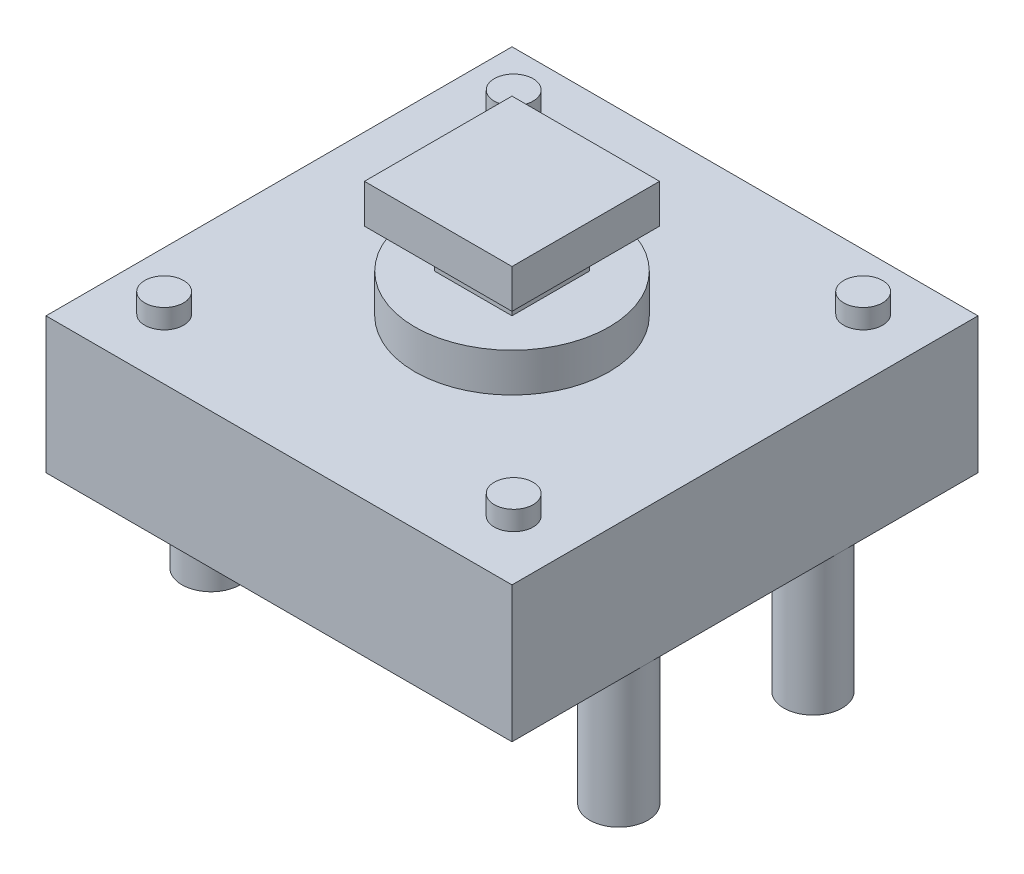
SolidWorks part; units mm, degrees
ref_plane "Front Plane" through (0, 0, 0) normal (0, 0, 1) x (1, 0, 0)
ref_plane "Top Plane" through (0, 0, 0) normal (0, 1, 0) x (1, 0, 0)
ref_plane "Right Plane" through (0, 0, 0) normal (1, 0, 0) x (0, 0, -1)
sketch "Sketch1" plane through (0, 0, 0) normal (0, 1, 0) x (1, 0, 0)
  line L1 (6, -6) -> (-6, -6)
  line L2 (6, -6) -> (6, 6)
  line L3 (6, 6) -> (-6, 6)
  line L4 (-6, -6) -> (-6, 6)
  line L5 (6, -6) -> (-6, 6) construction
  line L6 (6, 6) -> (-6, -6) construction
  point P0 (0, 0)
  dimension "D1" = 12
  dimension "D2" = 12
extrude "Boss-Extrude1" add sketch "Sketch1" along normal blind 3.5
sketch "Sketch2" plane through (0, 3.5, 0) normal (0, 1, 0) x (1, 0, 0)
  circle A0 centre (0, 0) radius 2.5
  dimension "D1" = 5
extrude "Boss-Extrude2" add sketch "Sketch2" along normal blind 1
sketch "Sketch3" plane through (0, 3.5, 0) normal (0, 1, 0) x (1, 0, 0)
  circle A8 centre (-4.5173, 4.5604) radius 0.5
  circle A9 centre (-4.5173, -4.4396) radius 0.5
  circle A10 centre (4.4827, -4.4396) radius 0.5
  circle A11 centre (4.4827, 4.5604) radius 0.5
extrude "Boss-Extrude3" add sketch "Sketch3" along normal blind 0.5
sketch "Sketch4" plane through (0, 4.5, 0) normal (0, 1, 0) x (1, 0, 0)
  line L1 (1, -1) -> (-1, -1)
  line L2 (1, -1) -> (1, 1)
  line L3 (1, 1) -> (-1, 1)
  line L4 (-1, -1) -> (-1, 1)
  line L5 (1, -1) -> (-1, 1) construction
  line L6 (1, 1) -> (-1, -1) construction
  point P0 (0, 0)
  dimension "D1" = 2
  dimension "D2" = 2
extrude "Boss-Extrude4" add sketch "Sketch4" along normal blind 1
sketch "Sketch5" plane through (0, 5.5, 0) normal (0, 1, 0) x (1, 0, 0)
  line L1 (1.9, -1.9) -> (-1.9, -1.9)
  line L2 (1.9, -1.9) -> (1.9, 1.9)
  line L3 (1.9, 1.9) -> (-1.9, 1.9)
  line L4 (-1.9, -1.9) -> (-1.9, 1.9)
  line L5 (1.9, -1.9) -> (-1.9, 1.9) construction
  line L6 (1.9, 1.9) -> (-1.9, -1.9) construction
  point P0 (0, 0)
  dimension "D1" = 3.8
  dimension "D2" = 3.8
extrude "Boss-Extrude5" add sketch "Sketch5" along normal blind 1
sketch "Sketch6" plane through (0, 0, 0) normal (0, -1, 0) x (1, 0, 0)
  line L0 (-6, -6) -> (-6, 6) construction
  line L1 (-6, 0) -> (6, 0) construction
  line L2 (6, 6) -> (6, -6) construction
  line L3 (0, 6) -> (0, -6) construction
  line L4 (-6, 6) -> (6, 6) construction
  line L5 (6, -6) -> (-6, -6) construction
  circle A0 centre (-5.25, 2.5) radius 0.75
  circle A1 centre (-5.25, -2.5) radius 0.75
  circle A2 centre (5.25, -2.5) radius 0.75
  circle A3 centre (5.25, 2.5) radius 0.75
  dimension "D1" = 1.5
  dimension "D2" = 2.5
extrude "Boss-Extrude6" add sketch "Sketch6" along normal blind 3.5
